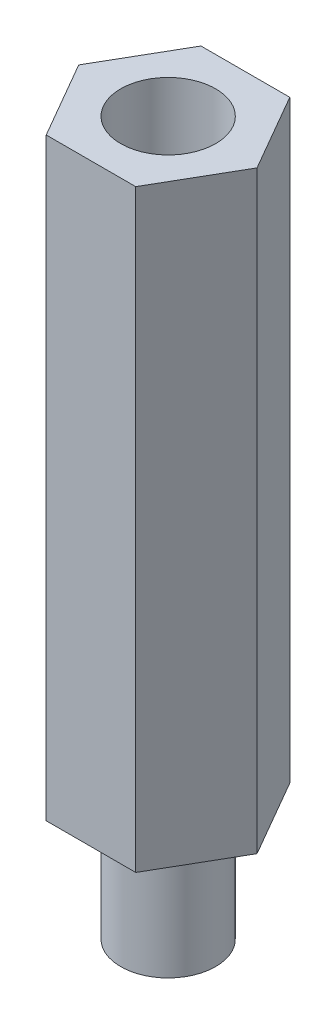
SolidWorks part; units mm, degrees
ref_plane "前视基准面" through (0, 0, 0) normal (0, 0, 1) x (1, 0, 0)
ref_plane "上视基准面" through (0, 0, 0) normal (0, 1, 0) x (1, 0, 0)
ref_plane "右视基准面" through (0, 0, 0) normal (1, 0, 0) x (0, 0, -1)
sketch "草图1" plane through (0, 0, 0) normal (0, 1, 0) x (1, 0, 0)
  line L0 (-3.0419, 3.9908) -> (4.4347, 3.9908)
  line L1 (4.4347, 3.9908) -> (8.202, -2.5342)
  line L2 (8.202, -2.5342) -> (4.4636, -9.0092)
  line L3 (4.4636, -9.0092) -> (-3.0708, -9.0092)
  line L4 (-3.0708, -9.0092) -> (-6.8092, -2.5342)
  line L5 (-6.8092, -2.5342) -> (-3.0419, 3.9908)
  line L6 (0.6964, 3.9908) -> (0.6964, -9.0092) construction
  line L7 (-6.8092, -2.5342) -> (8.202, -2.5342) construction
  circle A0 centre (0.6964, -2.5092) radius 4
  dimension "D6" = 8
  dimension "D1" = 13
  dimension "D2" = 13
  dimension "D3" = 13
  dimension "D4" = 120
  dimension "D5" = 120
extrude "凸台-拉伸1" add sketch "草图1" along normal blind 50
sketch "草图2" plane through (0, 0, 0) normal (0, -1, 0) x (1, 0, 0)
  circle A0 centre (0.6964, 2.5092) radius 4
extrude "凸台-拉伸2" add sketch "草图2" along normal blind 10 separate body
